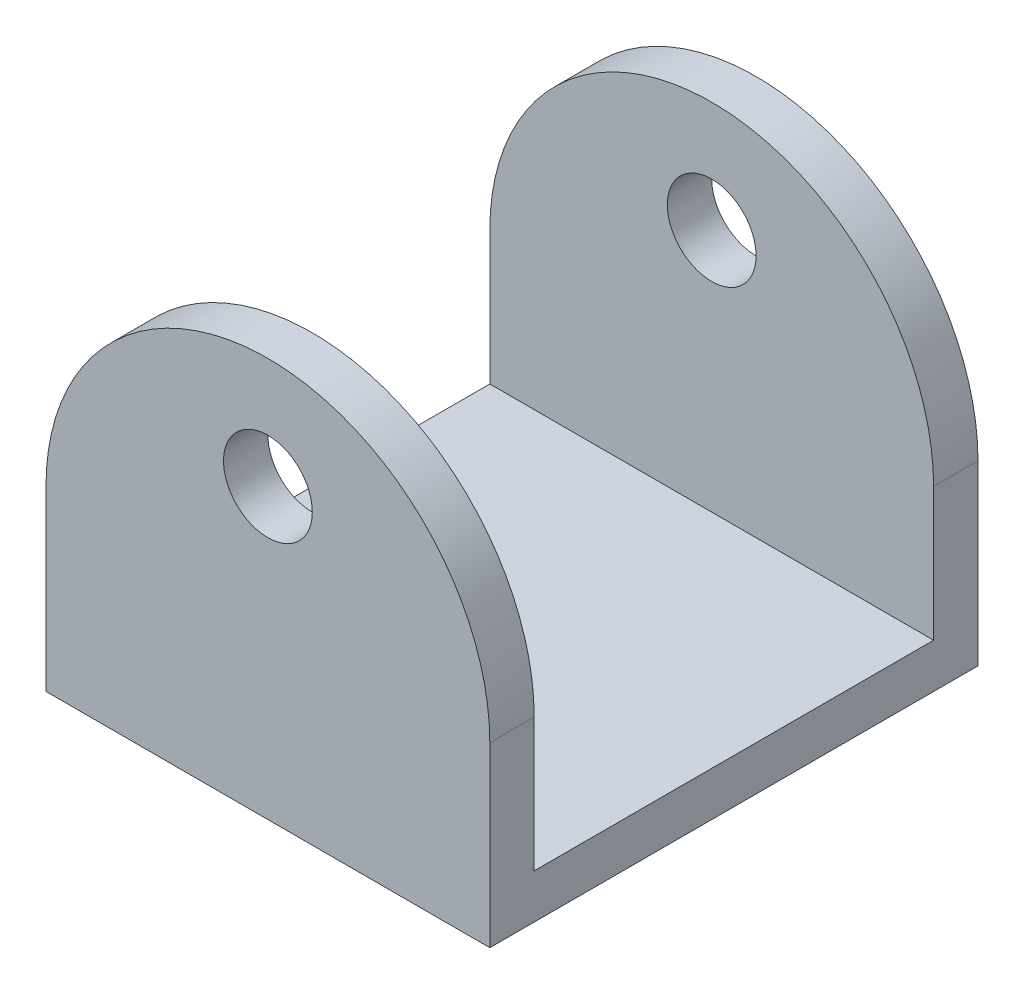
SolidWorks part; units mm, degrees
ref_plane "Front Plane" through (0, 0, 0) normal (0, 0, 1) x (1, 0, 0)
ref_plane "Top Plane" through (0, 0, 0) normal (0, 1, 0) x (1, 0, 0)
ref_plane "Right Plane" through (0, 0, 0) normal (1, 0, 0) x (0, 0, -1)
sketch "Sketch1" plane through (0, 0, 0) normal (0, 0, 1) x (1, 0, 0)
  line L0 (9.0365, -22.1029) -> (9.0365, 9.6471) construction
  line L2 (-22.7135, -22.1029) -> (-22.7135, -47.5029)
  line L3 (-22.7135, -47.5029) -> (40.7865, -47.5029)
  line L4 (40.7865, -22.1029) -> (40.7865, -47.5029)
  arc A0 (-22.7135, -22.1029) -> (40.7865, -22.1029) centre (9.0365, -22.1029) cw
  circle A1 centre (9.0365, -6.2279) radius 6.35
  dimension "D1" = 63.5
  dimension "D2" = 25.4
extrude "Boss-Extrude1" add sketch "Sketch1" along normal blind 69.85
sketch "Sketch2" plane through (-22.7135, 0, 0) normal (-1, 0, 0) x (0, 0, 1)
  line L0 (0, -22.1029) -> (0, -47.5029) construction
  line L1 (6.35, 13.3691) -> (63.5, 13.3691)
  line L2 (6.35, 13.3691) -> (6.35, -41.1529)
  line L3 (6.35, -41.1529) -> (63.5, -41.1529)
  line L4 (63.5, 13.3691) -> (63.5, -41.1529)
  line L5 (69.85, -22.1029) -> (69.85, -47.5029) construction
  line L6 (69.85, -47.5029) -> (0, -47.5029) construction
  dimension "D1" = 6.35
  dimension "D2" = 6.35
  dimension "D3" = 6.35
extrude "Cut-Extrude1" cut sketch "Sketch2" against normal through all both and the other way through all
